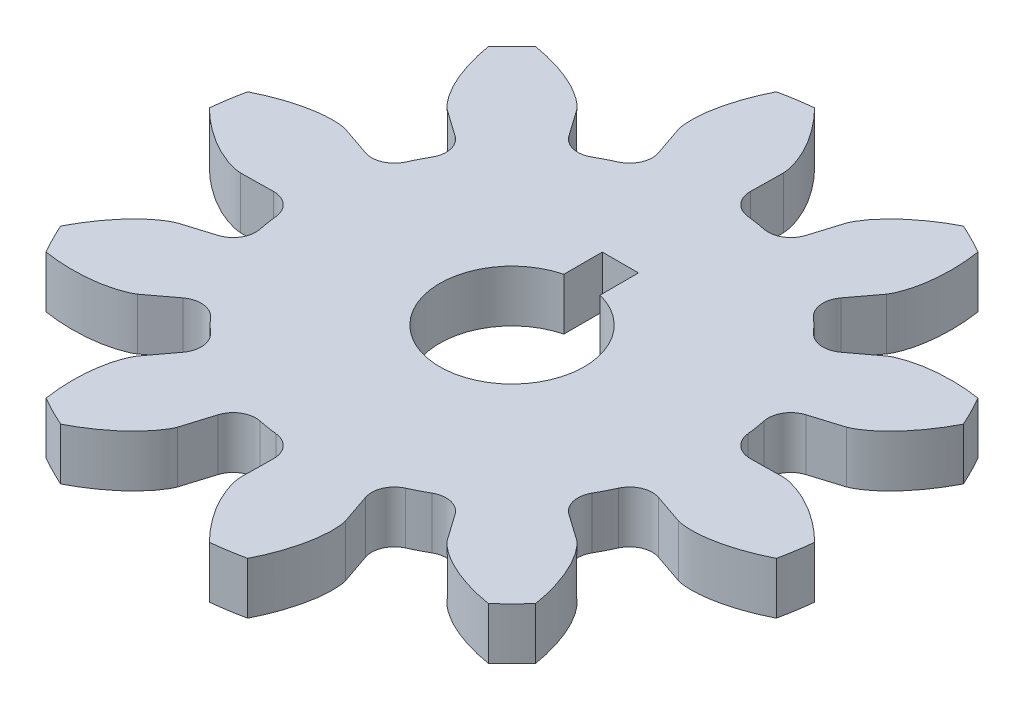
SolidWorks part; units mm, degrees
ref_plane "Front Plane" through (0, 0, 0) normal (0, 0, 1) x (1, 0, 0)
ref_plane "Top Plane" through (0, 0, 0) normal (0, 1, 0) x (1, 0, 0)
ref_plane "Right Plane" through (0, 0, 0) normal (1, 0, 0) x (0, 0, -1)
sketch "Sketch1" plane through (0, 0, 0) normal (0, 1, 0) x (1, 0, 0)
  line L0 (-25.5426, 23.7467) -> (25.8644, 23.7467) construction
  line L1 (0.6761, -1.2533) -> (0.6761, 42.4364) construction
  line L2 (-25.8752, 14.0828) -> (0.6761, 23.7467) construction
  line L3 (0.6761, 23.7467) -> (28.7461, 33.9634) construction
  line L4 (0.6761, -1.2533) -> (-7.3587, 20.8223) construction
  line L5 (-7.3587, 20.8223) -> (0.6761, 23.7467)
  line L6 (-11.8405, 18.6269) -> (0.6761, -1.2533) construction
  line L7 (-11.8405, 18.6269) -> (-0.3735, 25.8466)
  line L8 (-15.7574, 15.5344) -> (0.6761, -1.2533) construction
  line L9 (-15.7574, 15.5344) -> (-2.5012, 28.511)
  line L10 (0.6761, -1.2533) -> (-13.8813, 17.185) construction
  line L11 (-13.8813, 17.185) -> (-1.2839, 27.131)
  line L12 (0.6761, -1.2533) -> (-4.9685, 21.5508) construction
  line L13 (-4.9685, 21.5508) -> (0.9048, 23.0046)
  line L14 (0.6761, -1.2533) -> (-2.5144, 22.0214) construction
  line L15 (-2.5144, 22.0214) -> (1.0032, 22.5036)
  line L16 (0.6761, -1.2533) -> (-9.6581, 19.8439) construction
  line L17 (-9.6581, 19.8439) -> (0.2658, 24.705)
  line L18 (0.6761, -1.2533) -> (-17.1254, 14.0763) construction
  line L19 (-17.1254, 14.0763) -> (-3.7155, 29.6486)
  circle A0 centre (0.6761, -1.2533) radius 25
  circle A1 centre (0.6761, -1.2533) radius 23.4923 construction
  arc A2 (-7.3587, 20.8223) -> (-11.8405, 18.6269) centre (0.6761, -1.2533) ccw
  arc A3 (-7.3587, 20.8223) -> (-15.7574, 15.5344) centre (0.6761, -1.2533) ccw
  arc A4 (-7.3587, 20.8223) -> (-13.8813, 17.185) centre (0.6761, -1.2533) ccw
  arc A5 (-7.3587, 20.8223) -> (-4.9685, 21.5508) centre (0.6761, -1.2533) cw
  arc A6 (-7.3587, 20.8223) -> (-2.5144, 22.0214) centre (0.6761, -1.2533) cw
  arc A7 (-7.3587, 20.8223) -> (1.0262, 22.2364) centre (0.6761, -1.2533) cw
  arc A8 (-7.3587, 20.8223) -> (-9.6581, 19.8439) centre (0.6761, -1.2533) ccw
  arc A9 (-7.3587, 20.8223) -> (-17.1254, 14.0763) centre (0.6761, -1.2533) ccw
  dimension "D1" = 50
  dimension "D2" = 20
  dimension "D3" = 8.5505
  dimension "D5" = 13.5505
  dimension "D7" = 18.5505
  dimension "D9" = 16.0505
  dimension "D11" = 6.0505
  dimension "D13" = 3.5505
  dimension "D16" = 11.0505
  dimension "D18" = 20.5505
  dimension "D4" = 5
  dimension "D6" = 10
  dimension "D8" = 7.5
  dimension "D10" = 2.5
  dimension "D12" = 5
  dimension "D14" = 8.5505
  dimension "D15" = 2.5
  dimension "D17" = 12
sketch "Sketch2" plane through (0, 0, 0) normal (0, 1, 0) x (1, 0, 0)
  line L0 (0.6761, -1.2533) -> (-4.0169, 28.3774) construction
  line L1 (0.6761, -1.2533) -> (0.6761, 42.4364) construction
  line L2 (0.6761, -1.2533) -> (-6.9156, 20.9786) construction
  line L3 (0.6761, -1.2533) -> (1.0262, 22.2364) construction
  line L4 (-6.9156, 20.9786) -> (-3.3613, 10.5699)
  line L5 (1.0262, 22.2364) -> (0.8623, 11.2376)
  line L6 (-3.3613, 10.5699) -> (0.8623, 11.2376)
  arc A1 (-2.5607, 28.5716) -> (-5.4612, 28.1122) centre (0.6761, -1.2533) ccw
  spline S0 degree 3 poles (-2.5607, 28.5716) (-2.5408, 28.5514) (-2.0905, 28.0937) (-1.3154, 27.2192) (-0.3994, 25.9352) (0.2449, 24.7937) (0.6606, 23.8354) (0.9195, 23.0079) (1.0163, 22.4964) (1.0262, 22.2364) knots 0.17575 0.17575 0.17575 0.17575 0.185197 0.390017 0.565239 0.710864 0.826892 0.913323 1 1 1 1
  spline S1 degree 3 poles (-5.4612, 28.1122) (-5.4739, 28.0869) (-5.7686, 27.5108) (-6.2255, 26.4417) (-6.7033, 24.9367) (-6.9626, 23.6522) (-7.0621, 22.6123) (-7.0525, 21.7453) (-6.9865, 21.2289) (-6.9156, 20.9786) knots 0.17575 0.17575 0.17575 0.17575 0.185197 0.390017 0.565239 0.710864 0.826892 0.913323 1 1 1 1
  dimension "D1" = 9
sketch "Sketch3" plane through (0, 0, 0) normal (0, 1, 0) x (1, 0, 0)
  circle A0 centre (0.6761, -1.2533) radius 18.75
extrude "Boss-Extrude1" add sketch "Sketch3" along normal blind 4.5542 contours A0
extrude "Boss-Extrude3" add sketch "Sketch2" along normal up to surface (4.5542 mm away) up to face at (0.6761, 4.5542, 20.0033)
fillet "Fillet1" radius 2 2 edges at (0.9555, 2.2771, -17.4946) (-5.3831, 2.2771, -16.4907)
pattern_circular "CirPattern2" count 10 over 360 about axis through (0.6761, 4.5542, 1.2533) along (0, -1, 0) of "Boss-Extrude3", "Fillet1"
sketch "Sketch8" plane through (0, 4.5542, 0) normal (0, 1, 0) x (1, 0, 0)
  circle A0 centre (0.6761, -1.2533) radius 6.35
extrude "Cut-Extrude3" cut sketch "Sketch8" against normal through all
sketch "Sketch10" plane through (0, 4.5542, 0) normal (0, 1, 0) x (1, 0, 0)
  line L0 (-0.9114, -1.2533) -> (2.2636, -1.2533)
  line L2 (-0.9114, -1.2533) -> (-0.9114, 8.2717)
  line L3 (-0.9114, 8.2717) -> (2.2636, 8.2717)
  line L4 (2.2636, -1.2533) -> (2.2636, 8.2717)
  line L5 (0.6761, 8.2717) -> (0.6761, -1.2533) construction
  line L6 (-0.9114, -1.2533) -> (2.2636, -1.2533) construction
  point P0 (0.6761, -1.2533)
extrude "Cut-Extrude5" cut sketch "Sketch10" against normal through all
sketch "Sketch11" plane through (0, 4.5542, 0) normal (0, 1, 0) x (1, 0, 0)
  circle A0 centre (0.6761, -1.2533) radius 25
equation "\"D5@Sketch1\"=\"D3@Sketch1\"+\"D4@Sketch1\""
equation "\"D7@Sketch1\"=\"D3@Sketch1\"+\"D6@Sketch1\""
equation "\"D9@Sketch1\"=\"D3@Sketch1\"+\"D8@Sketch1\""
equation "\"D11@Sketch1\"=\"D3@Sketch1\"-\"D10@Sketch1\""
equation "\"D13@Sketch1\"=\"D3@Sketch1\"-\"D12@Sketch1\""
equation "\"D14@Sketch1\"=\"D3@Sketch1\""
equation "\"D16@Sketch1\"=\"D3@Sketch1\"+\"D15@Sketch1\""
equation "\"D1@Sketch2\"=360/10/4"
equation "\"D18@Sketch1\"=\"D3@Sketch1\"+\"D17@Sketch1\""
